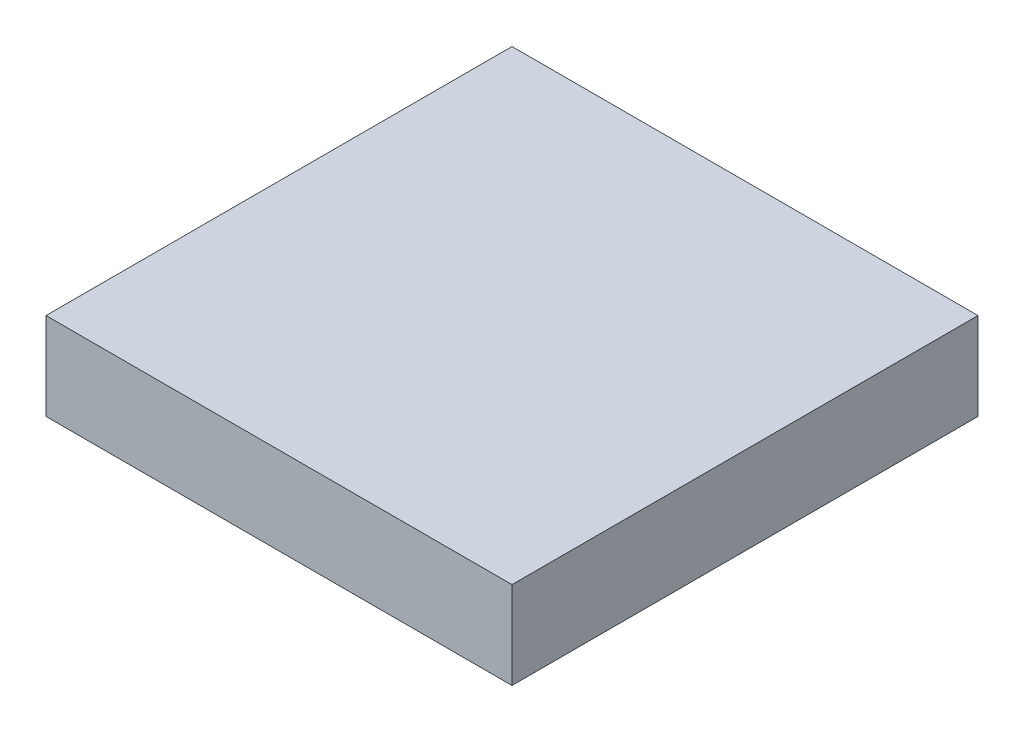
SolidWorks part; units mm, degrees
ref_plane "Front Plane" through (0, 0, 0) normal (0, 0, 1) x (1, 0, 0)
ref_plane "Top Plane" through (0, 0, 0) normal (0, 1, 0) x (1, 0, 0)
ref_plane "Right Plane" through (0, 0, 0) normal (1, 0, 0) x (0, 0, -1)
sketch "Sketch1" plane through (0, 0, 0) normal (0, 1, 0) x (1, 0, 0)
  line L1 (-8, -8) -> (8, -8)
  line L2 (-8, -8) -> (-8, 8)
  line L3 (-8, 8) -> (8, 8)
  line L4 (8, -8) -> (8, 8)
  line L5 (-8, -8) -> (8, 8) construction
  line L6 (-8, 8) -> (8, -8) construction
  point P0 (0, 0)
  dimension "D1" = 16
  dimension "D2" = 16
extrude "Boss-Extrude1" add sketch "Sketch1" along normal blind 3
sketch "Sketch2" plane through (0, 0, 0) normal (0, -1, 0) x (1, 0, 0)
  line L1 (-6, -6) -> (6, -6)
  line L2 (-6, -6) -> (-6, 6)
  line L3 (-6, 6) -> (6, 6)
  line L4 (6, -6) -> (6, 6)
  line L5 (-6, -6) -> (6, 6) construction
  line L6 (-6, 6) -> (6, -6) construction
  circle A0 centre (0, 0) radius 2.5
  point P0 (0, 0)
  dimension "D1" = 5
  dimension "D2" = 12
  dimension "D3" = 12
extrude "Cut-Extrude1" cut sketch "Sketch2" against normal blind 2
sketch "Sketch3" plane through (0, 0, 0) normal (0, -1, 0) x (1, 0, 0)
  line L0 (8, -8) -> (-8, -8) construction
  line L1 (8, 8) -> (8, -8) construction
  line L2 (-8, -8) -> (-8, 8) construction
  line L3 (-8, 8) -> (8, 8) construction
  circle A0 centre (-7, 7) radius 0.75
  circle A1 centre (7, 7) radius 0.75
  circle A2 centre (7, -7) radius 0.75
  circle A3 centre (-7, -7) radius 0.75
  dimension "D1" = 1.5
  dimension "D2" = 1.5
  dimension "D3" = 1.5
  dimension "D4" = 1.5
  dimension "D5" = 1
  dimension "D6" = 1
  dimension "D7" = 1
  dimension "D8" = 1
  dimension "D9" = 1
  dimension "D10" = 1
  dimension "D11" = 1
  dimension "D12" = 1
extrude "Cut-Extrude2" cut sketch "Sketch3" against normal blind 2
